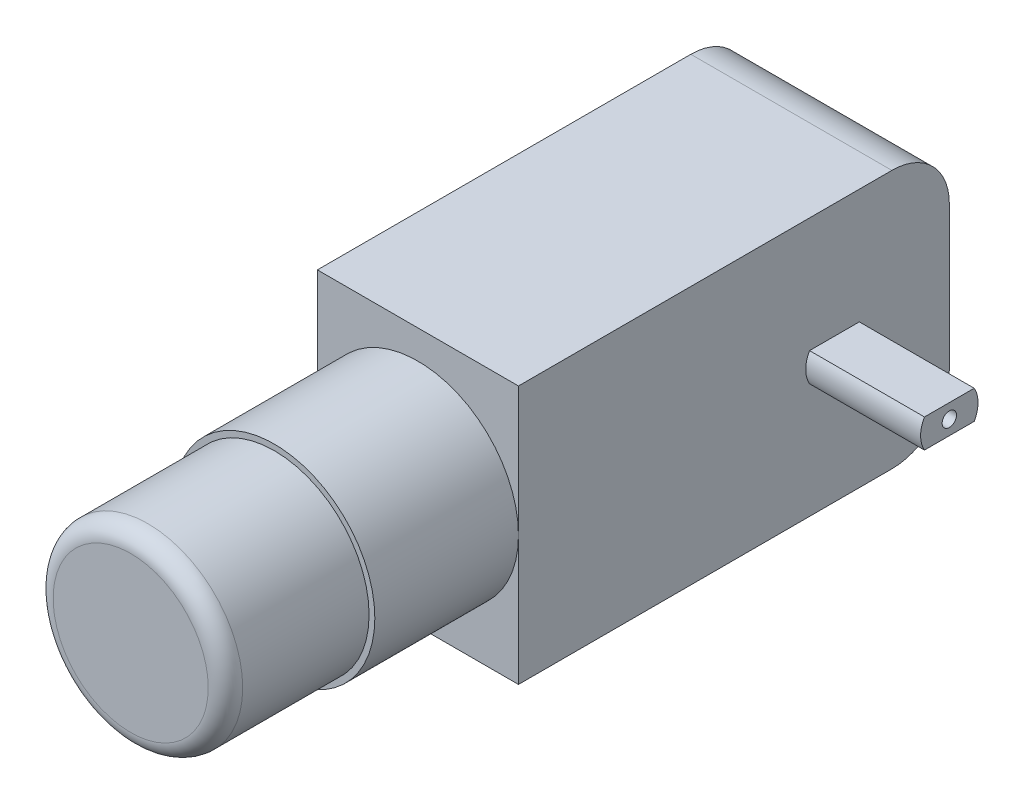
SolidWorks part; units mm, degrees
ref_plane "Front Plane" through (0, 0, 0) normal (0, 0, 1) x (1, 0, 0)
ref_plane "Top Plane" through (0, 0, 0) normal (0, 1, 0) x (1, 0, 0)
ref_plane "Right Plane" through (0, 0, 0) normal (1, 0, 0) x (0, 0, -1)
sketch "Sketch1" plane through (0, 0, 0) normal (1, 0, 0) x (0, 0, -1)
  line L1 (-18.75, -11.25) -> (18.75, -11.25)
  line L2 (-18.75, -11.25) -> (-18.75, 11.25)
  line L3 (-18.75, 11.25) -> (18.75, 11.25)
  line L4 (18.75, -11.25) -> (18.75, 11.25)
  line L5 (-18.75, -11.25) -> (18.75, 11.25) construction
  line L6 (-18.75, 11.25) -> (18.75, -11.25) construction
  point P0 (0, 0)
  point P8 (12.5, 0)
  dimension "D1" = 37.5
  dimension "D2" = 22.5
extrude "Boss-Extrude2" add sketch "Sketch1" along normal blind 17.5
ref_plane "Plane1" through (17.5, 0, 0) normal (1, 0, 0) x (0, 0, -1)
sketch "Sketch2" plane through (17.5, 0, 0) normal (1, 0, 0) x (0, 0, -1)
  line L0 (18.75, -11.25) -> (18.75, 11.25) construction
  line L1 (6.5849, 1.2465) -> (10.9151, 1.2465)
  line L2 (6.25, -0.0035) -> (11.25, -0.0035)
  line L3 (6.5849, -1.2535) -> (10.9151, -1.2535)
  circle A0 centre (8.75, -0.0035) radius 2.5
  circle A1 centre (8.75, -0.0035) radius 0.625
  dimension "D1" = 5
  dimension "D4" = 1.25
  dimension "D2" = 10
  dimension "D3" = 2.5
extrude "Boss-Extrude3" add sketch "Sketch2" along normal blind 10 contours L2 A0 L1 | L2 A0 L3
ref_plane "Plane2" through (0, 0, 18.75) normal (0, 0, 1) x (1, 0, 0)
sketch "Sketch3" plane through (0, 0, 18.75) normal (0, 0, 1) x (1, 0, 0)
  circle A0 centre (8.75, 0) radius 8.75
extrude "Boss-Extrude4" add sketch "Sketch3" along normal blind 12.5
ref_plane "Plane4" through (0, 0, 31.25) normal (0, 0, 1) x (1, 0, 0)
sketch "Sketch4" plane through (0, 0, 31.25) normal (0, 0, 1) x (1, 0, 0)
  circle A0 centre (8.75, 0) radius 8.25
  circle A1 centre (8.75, 0) radius 8.75 construction
  dimension "D1" = 0.5
extrude "Boss-Extrude5" add sketch "Sketch4" along normal blind 12.5
fillet "Fillet2" radius 1.5 1 edges at (17, 0, 43.75)
fillet "Fillet3" radius 5 2 edges at (8.75, -11.25, -18.75) (8.75, 11.25, -18.75)
ref_plane "Plane5" through (0, 0, 0) normal (-1, 0, 0) x (0, 0, 1)
sketch "Sketch5" plane through (0, 0, 0) normal (-1, 0, 0) x (0, 0, 1)
  line L1 (-11.25, 0) -> (-6.25, 0)
  line L2 (-10.9151, 1.25) -> (-6.5849, 1.25)
  line L3 (-10.9151, -1.25) -> (-6.5849, -1.25)
  line L4 (-18.75, 0) -> (-8.75, 0)
  line L5 (-18.75, -6.25) -> (-18.75, 6.25) construction
  circle A0 centre (-8.75, 0) radius 2.5
  dimension "D1" = 5
  dimension "D2" = 90
  dimension "D3" = 2.5
  dimension "D4" = 10
extrude "Boss-Extrude6" add sketch "Sketch5" along normal blind 10 contours L1 A0 L2 | L1 A0 L3
